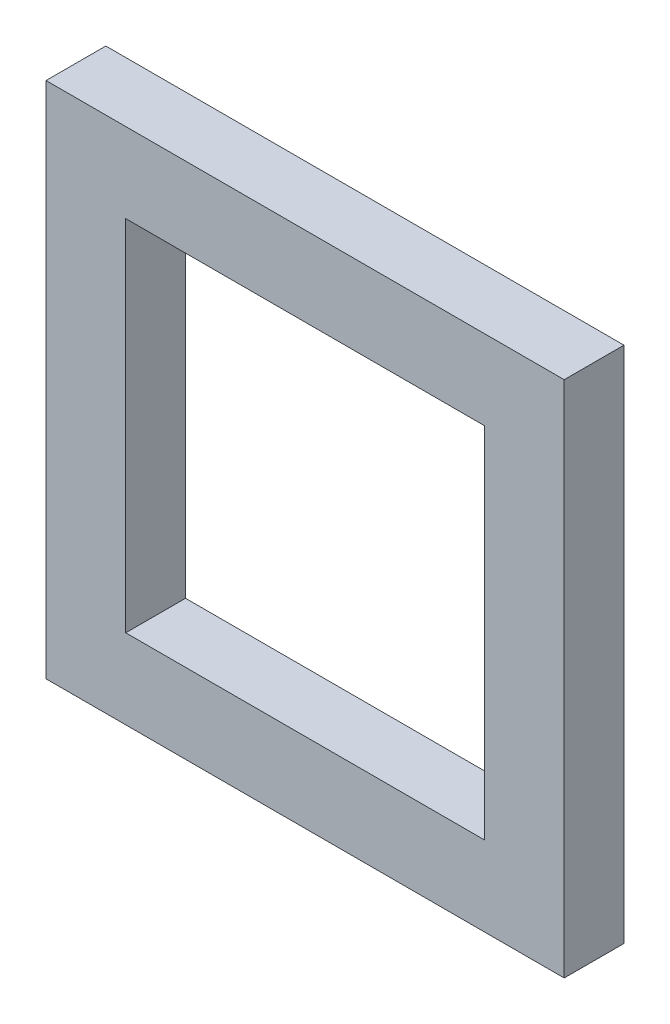
SolidWorks part; units mm, degrees
ref_plane "Front Plane" through (0, 0, 0) normal (0, 0, 1) x (1, 0, 0)
ref_plane "Top Plane" through (0, 0, 0) normal (0, 1, 0) x (1, 0, 0)
ref_plane "Right Plane" through (0, 0, 0) normal (1, 0, 0) x (0, 0, -1)
sketch "Sketch1" plane through (0, 0, 0) normal (0, 0, 1) x (1, 0, 0)
  line L1 (4.5, -4.5) -> (-4.5, -4.5)
  line L2 (4.5, -4.5) -> (4.5, 4.5)
  line L3 (4.5, 4.5) -> (-4.5, 4.5)
  line L4 (-4.5, -4.5) -> (-4.5, 4.5)
  line L5 (4.5, -4.5) -> (-4.5, 4.5) construction
  line L6 (4.5, 4.5) -> (-4.5, -4.5) construction
  line L7 (6.5, -6.5) -> (-6.5, -6.5)
  line L8 (6.5, -6.5) -> (6.5, 6.5)
  line L9 (6.5, 6.5) -> (-6.5, 6.5)
  line L10 (-6.5, -6.5) -> (-6.5, 6.5)
  point P0 (0, 0)
  point P6 (0, 0)
  dimension "D1" = 9
  dimension "D2" = 2
  dimension "D3" = 2
  dimension "D4" = 2
  dimension "D5" = 2
extrude "Boss-Extrude1" add sketch "Sketch1" along normal blind 1.5
